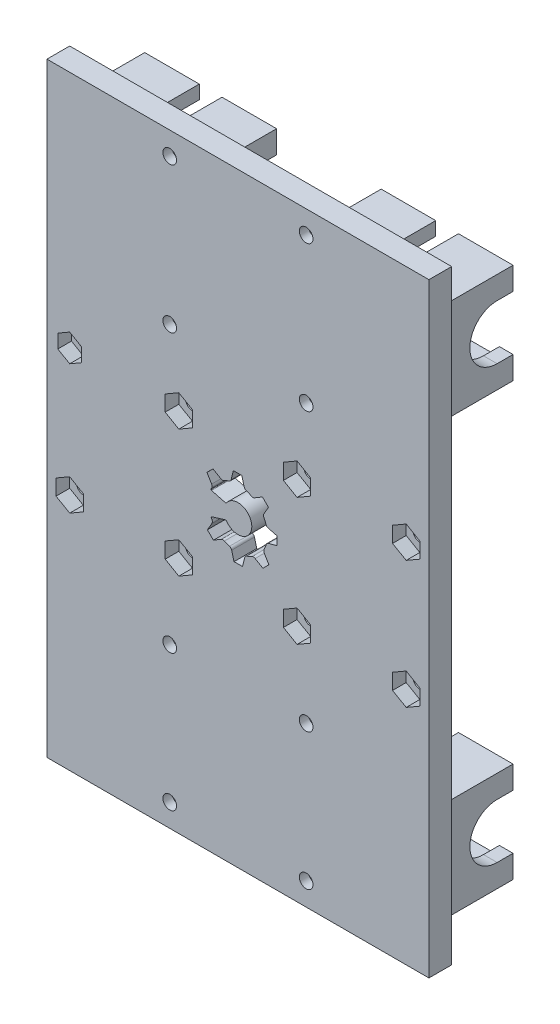
SolidWorks part; units mm, degrees
ref_plane "Alzado" through (0, 0, 0) normal (0, 0, 1) x (1, 0, 0)
ref_plane "Planta" through (0, 0, 0) normal (0, 1, 0) x (1, 0, 0)
ref_plane "Vista lateral" through (0, 0, 0) normal (1, 0, 0) x (0, 0, -1)
sketch "Croquis1" plane through (0, 0, 0) normal (0, 0, 1) x (1, 0, 0)
  line L0 (0, 0) -> (84, 0)
  line L1 (84, 0) -> (84, 133)
  line L2 (84, 133) -> (0, 133)
  line L3 (0, 133) -> (0, 0)
  circle A6 centre (57, 5) radius 1.5
  circle A7 centre (27, 5) radius 1.5
  circle A8 centre (27, 35) radius 1.5
  circle A9 centre (57, 35) radius 1.5
  circle A10 centre (57, 128) radius 1.5
  circle A11 centre (27, 128) radius 1.5
  circle A12 centre (27, 96) radius 1.5
  circle A13 centre (57, 96) radius 1.5
  circle A14 centre (5, 80.5) radius 1.5
  circle A15 centre (29, 80.5) radius 1.5
  circle A16 centre (29, 52.5) radius 1.5
  circle A17 centre (5, 52.5) radius 1.5
  circle A18 centre (79, 52.5) radius 1.5
  circle A19 centre (55, 52.5) radius 1.5
  circle A20 centre (55, 80.5) radius 1.5
  circle A21 centre (79, 80.5) radius 1.5
  dimension "D8" = 3
  dimension "D5" = 3
  dimension "D12" = 3
  dimension "D1" = 84
  dimension "D2" = 133
  dimension "D6" = 2
  dimension "D9" = 2
  dimension "D10" = 2
  dimension "D11" = 2
  dimension "D14" = 2
  dimension "D15" = 2
extrude "Saliente-Extruir1" add sketch "Croquis1" along normal blind 5
sketch "agujeros tuercas" plane through (0, 0, 0) normal (0, 0, -1) x (-1, 0, 0)
  line L44 (-57, 131) -> (-59.5981, 129.5)
  line L45 (-59.5981, 129.5) -> (-59.5981, 126.5)
  line L46 (-59.5981, 126.5) -> (-57, 125)
  line L47 (-57, 125) -> (-54.4019, 126.5)
  line L48 (-54.4019, 126.5) -> (-54.4019, 129.5)
  line L49 (-54.4019, 129.5) -> (-57, 131)
  line L50 (-27, 131) -> (-29.5981, 129.5)
  line L51 (-29.5981, 129.5) -> (-29.5981, 126.5)
  line L52 (-29.5981, 126.5) -> (-27, 125)
  line L53 (-27, 125) -> (-24.4019, 126.5)
  line L54 (-24.4019, 126.5) -> (-24.4019, 129.5)
  line L55 (-24.4019, 129.5) -> (-27, 131)
  line L68 (-27, 99) -> (-29.5981, 97.5)
  line L69 (-29.5981, 97.5) -> (-29.5981, 94.5)
  line L70 (-29.5981, 94.5) -> (-27, 93)
  line L71 (-27, 93) -> (-24.4019, 94.5)
  line L72 (-24.4019, 94.5) -> (-24.4019, 97.5)
  line L73 (-24.4019, 97.5) -> (-27, 99)
  line L164 (-57, 99) -> (-59.5981, 97.5)
  line L165 (-59.5981, 97.5) -> (-59.5981, 94.5)
  line L166 (-59.5981, 94.5) -> (-57, 93)
  line L167 (-57, 93) -> (-54.4019, 94.5)
  line L168 (-54.4019, 94.5) -> (-54.4019, 97.5)
  line L169 (-54.4019, 97.5) -> (-57, 99)
  line L218 (-57, 38) -> (-59.5981, 36.5)
  line L219 (-59.5981, 36.5) -> (-59.5981, 33.5)
  line L220 (-59.5981, 33.5) -> (-57, 32)
  line L221 (-57, 32) -> (-54.4019, 33.5)
  line L222 (-54.4019, 33.5) -> (-54.4019, 36.5)
  line L223 (-54.4019, 36.5) -> (-57, 38)
  line L224 (-27, 38) -> (-29.5981, 36.5)
  line L225 (-29.5981, 36.5) -> (-29.5981, 33.5)
  line L226 (-29.5981, 33.5) -> (-27, 32)
  line L227 (-27, 32) -> (-24.4019, 33.5)
  line L228 (-24.4019, 33.5) -> (-24.4019, 36.5)
  line L229 (-24.4019, 36.5) -> (-27, 38)
  line L230 (-57, 8) -> (-59.5981, 6.5)
  line L231 (-59.5981, 6.5) -> (-59.5981, 3.5)
  line L232 (-59.5981, 3.5) -> (-57, 2)
  line L233 (-57, 2) -> (-54.4019, 3.5)
  line L234 (-54.4019, 3.5) -> (-54.4019, 6.5)
  line L235 (-54.4019, 6.5) -> (-57, 8)
  line L236 (-27, 8) -> (-29.5981, 6.5)
  line L237 (-29.5981, 6.5) -> (-29.5981, 3.5)
  line L238 (-29.5981, 3.5) -> (-27, 2)
  line L239 (-27, 2) -> (-24.4019, 3.5)
  line L240 (-24.4019, 3.5) -> (-24.4019, 6.5)
  line L241 (-24.4019, 6.5) -> (-27, 8)
  circle A1 centre (-57, 128) radius 3 construction
  circle A2 centre (-27, 128) radius 2.5981 construction
  circle A4 centre (-57, 96) radius 3 construction
  circle A5 centre (-27, 96) radius 3 construction
  circle A14 centre (-57, 35) radius 3 construction
  circle A15 centre (-27, 35) radius 3 construction
  circle A16 centre (-57, 5) radius 3 construction
  circle A17 centre (-27, 5) radius 3 construction
sketch "Croquis3" plane through (0, 0, 0) normal (0, 0, -1) x (-1, 0, 0)
  line L0 (-82.5, 125) -> (-82.5, 103)
  line L1 (-82.5, 125) -> (-53.5, 125)
  line L2 (-82.5, 103) -> (-53.5, 103)
  line L3 (-53.5, 103) -> (-53.5, 125)
  line L4 (-84, 0) -> (-84, 133) construction
  line L5 (-84, 133) -> (0, 133) construction
  line L6 (-30.5, 125) -> (-30.5, 103)
  line L7 (-30.5, 103) -> (-1.5, 103)
  line L8 (-1.5, 103) -> (-1.5, 125)
  line L9 (-1.5, 125) -> (-30.5, 125)
  line L10 (0, 133) -> (0, 0) construction
  line L11 (10, 114) -> (-94, 114) construction
  line L17 (-82.5, 30) -> (-82.5, 8)
  line L18 (-82.5, 30) -> (-53.5, 30)
  line L19 (-82.5, 8) -> (-53.5, 8)
  line L20 (-53.5, 8) -> (-53.5, 30)
  line L21 (-30.5, 30) -> (-30.5, 8)
  line L22 (-30.5, 8) -> (-1.5, 8)
  line L23 (-1.5, 8) -> (-1.5, 30)
  line L24 (-1.5, 30) -> (-30.5, 30)
  line L25 (10, 19) -> (-94, 19) construction
  dimension "D1" = 22
  dimension "D2" = 29
  dimension "D3" = 1.5
  dimension "D4" = 8
  dimension "D5" = 1.5
  dimension "D6" = 8
  dimension "D7" = 29
  dimension "D8" = 22
  dimension "D9" = 2
extrude "Saliente-Extruir2" add sketch "Croquis3" along normal blind 15
sketch "Croquis4" plane through (1.5, 0, 0) normal (-1, 0, 0) x (0, 0, 1)
  line L0 (0, 133) -> (0, 0) construction
  line L2 (-11.5, 25) -> (-15, 25)
  line L3 (-11.5, 120) -> (-15, 120)
  line L4 (-15, 103) -> (-15, 125) construction
  line L5 (-15, 120) -> (-15, 108)
  line L6 (-15, 108) -> (-11.5, 108)
  line L7 (-15, 25) -> (-15, 13)
  line L8 (-15, 13) -> (-11.5, 13)
  arc A0 (-11.5, 108) -> (-11.5, 120) centre (-11.5, 114) ccw
  arc A1 (-11.5, 13) -> (-11.5, 25) centre (-11.5, 19) ccw
  dimension "D2" = 6
  dimension "D1" = 11.5
  dimension "D3" = 2
extrude "agujero rodamientos" cut sketch "Croquis4" against normal up to surface (81 mm away) up to face at (82.5, 114, -7.5)
ref_plane "Plano1" through (4.5, 0, 0) normal (-1, 0, 0) x (0, 0, 1)
ref_plane "Plano3" through (56.5, 0, 0) normal (-1, 0, 0) x (0, 0, 1)
sketch "Croquis5" plane through (56.5, 0, 0) normal (-1, 0, 0) x (0, 0, 1)
  line L0 (-11.5, 122) -> (-15, 122)
  line L1 (-15, 120) -> (-15, 125) construction
  line L2 (-15, 122) -> (-15, 106)
  line L4 (-11.5, 106) -> (-15, 106)
  arc A1 (-11.5, 106) -> (-11.5, 122) centre (-11.5, 114) ccw
extrude "Cortar-Extruir3" cut sketch "Croquis5" against normal offset from surface (23 mm away) 3 up to face at (82.5, 114, -9.625)
sketch "Croquis6" plane through (4.5, 0, 0) normal (-1, 0, 0) x (0, 0, 1)
  line L0 (-11.5, 122) -> (-15, 122)
  line L1 (-11.5, 106) -> (-15, 106)
  line L2 (-15, 106) -> (-15, 122)
  arc A1 (-11.5, 106) -> (-11.5, 122) centre (-11.5, 114) ccw
extrude "Cortar-Extruir4" cut sketch "Croquis6" against normal offset from surface (23 mm away) 3 up to face at (30.5, 114, -9.625)
ref_plane "Plano4" through (56.5, 0, 0) normal (-1, 0, 0) x (0, 0, 1)
sketch "Croquis7" plane through (56.5, 0, 0) normal (-1, 0, 0) x (0, 0, 1)
  line L0 (-11.5, 27) -> (-15, 27)
  line L1 (-15, 25) -> (-15, 30) construction
  line L2 (-11.5, 11) -> (-15, 11)
  line L3 (-15, 8) -> (-15, 13) construction
  line L4 (-15, 11) -> (-15, 27)
  arc A1 (-11.5, 11) -> (-11.5, 27) centre (-11.5, 19) ccw
extrude "Cortar-Extruir5" cut sketch "Croquis7" against normal offset from surface (23 mm away) 3 up to face at (82.5, 19, -9.625)
ref_plane "Plano5" through (4.5, 0, 0) normal (-1, 0, 0) x (0, 0, 1)
sketch "Croquis8" plane through (4.5, 0, 0) normal (-1, 0, 0) x (0, 0, 1)
  line L0 (-11.5, 27) -> (-15, 27)
  line L1 (-15, 27) -> (-15, 11)
  line L2 (-15, 11) -> (-11.5, 11)
  arc A1 (-11.5, 11) -> (-11.5, 27) centre (-11.5, 19) ccw
extrude "Cortar-Extruir6" cut sketch "Croquis8" against normal offset from surface (23 mm away) 3 up to face at (30.5, 19, -9.625)
sketch "Croquis9" plane through (0, 125, 0) normal (0, 1, 0) x (1, 0, 0)
  line L0 (13.5, 15) -> (18.5, 15)
  line L1 (65.5, 15) -> (70.5, 15)
  line L2 (1.5, 15) -> (30.5, 15) construction
  line L3 (18.5, 15) -> (18.5, 7.5)
  line L4 (18.5, 7.5) -> (13.5, 7.5)
  line L5 (13.5, 7.5) -> (13.5, 15)
  line L6 (13.5, 3) -> (18.5, 3)
  line L7 (18.5, 3) -> (18.5, 0)
  line L8 (84, 0) -> (0, 0) construction
  line L9 (18.5, 0) -> (13.5, 0)
  line L10 (1.5, 0) -> (30.5, 0) construction
  line L11 (13.5, 0) -> (13.5, 3)
  line L12 (53.5, 15) -> (82.5, 15) construction
  line L13 (70.5, 15) -> (70.5, 7.5)
  line L14 (70.5, 7.5) -> (65.5, 7.5)
  line L15 (65.5, 7.5) -> (65.5, 15)
  line L16 (65.5, 3) -> (70.5, 3)
  line L17 (70.5, 3) -> (70.5, 0)
  line L18 (53.5, 0) -> (82.5, 0) construction
  line L19 (70.5, 0) -> (65.5, 0)
  line L20 (65.5, 0) -> (65.5, 3)
  dimension "D1" = 4.5
  dimension "D2" = 7.5
  dimension "D3" = 5
  dimension "D5" = 7.5
  dimension "D6" = 5
extrude "Cortar-Extruir7" cut sketch "Croquis9" against normal through all
sketch "Croquis10" plane through (0, 0, 0) normal (0, 0, 1) x (1, 0, 0)
  line L0 (42, 133) -> (42, 0) construction
  line L2 (35.1881, 71.8847) -> (36.5015, 73.2203)
  line L3 (40.9908, 75.1242) -> (42.864, 75.14)
  line L4 (47.3847, 73.3119) -> (48.7203, 71.9985)
  line L5 (50.6242, 67.5092) -> (50.64, 65.636)
  line L6 (48.8119, 61.1153) -> (47.4985, 59.7797)
  line L7 (36.2096, 63.9479) -> (39.384, 64.9286)
  line L8 (35.1881, 71.8847) -> (36.2199, 70.1785)
  line L9 (43.0092, 57.8758) -> (41.136, 57.86)
  line L10 (36.6153, 59.6881) -> (35.2797, 61.0015)
  line L11 (36.5015, 73.2203) -> (38.2249, 72.2174)
  line L12 (40.9908, 75.1242) -> (40.5139, 73.1882)
  line L13 (42.864, 75.14) -> (43.3734, 73.2122)
  line L14 (47.3847, 73.3119) -> (45.6785, 72.2801)
  line L15 (48.7203, 71.9985) -> (47.7174, 70.2751)
  line L16 (50.6242, 67.5092) -> (48.6882, 67.9861)
  line L17 (50.64, 65.636) -> (48.7122, 65.1266)
  line L18 (48.8119, 61.1153) -> (47.7801, 62.8215)
  line L19 (47.4985, 59.7797) -> (45.7751, 60.7826)
  line L20 (43.0092, 57.8758) -> (43.4861, 59.8118)
  line L21 (41.136, 57.86) -> (40.6266, 59.7878)
  line L22 (36.6153, 59.6881) -> (38.3215, 60.7199)
  line L23 (35.2797, 61.0015) -> (36.2826, 62.7249)
  line L24 (39.4066, 68.1085) -> (36.1706, 68.9523)
  line L25 (84, 133) -> (0, 133) construction
  line L26 (0, 0) -> (84, 0) construction
  line L27 (84, 66.5) -> (0, 66.5) construction
  line L28 (84, 0) -> (84, 133) construction
  line L29 (0, 133) -> (0, 0) construction
  arc A0 (43.9667, 60.3256) -> (45.0717, 60.7943) centre (42, 66.5) ccw
  arc A1 (36.127, 63.7617) -> (36.2943, 63.4283) centre (42, 66.5) ccw
  arc A2 (36.2096, 63.9479) -> (36.127, 63.7617) centre (36.2495, 63.8188) ccw
  arc A3 (36.0813, 69.1381) -> (36.1706, 68.9523) centre (36.2047, 69.0831) ccw
  arc A4 (38.9283, 72.2057) -> (38.2249, 72.2174) centre (38.587, 72.8397) cw
  arc A5 (36.2434, 69.4753) -> (36.2199, 70.1785) centre (35.6038, 69.8059) ccw
  arc A6 (43.8625, 72.7066) -> (43.3734, 73.2122) centre (44.0695, 73.3962) cw
  arc A7 (40.0333, 72.6744) -> (40.5139, 73.1882) centre (39.8148, 73.3604) ccw
  arc A8 (47.7057, 69.5717) -> (47.7174, 70.2751) centre (48.3397, 69.913) cw
  arc A9 (44.9753, 72.2566) -> (45.6785, 72.2801) centre (45.3059, 72.8962) ccw
  arc A10 (48.2066, 64.6375) -> (48.7122, 65.1266) centre (48.8962, 64.4305) cw
  arc A11 (48.1744, 68.4667) -> (48.6882, 67.9861) centre (48.8604, 68.6852) ccw
  arc A12 (45.0717, 60.7943) -> (45.7751, 60.7826) centre (45.413, 60.1603) cw
  arc A13 (47.7566, 63.5247) -> (47.7801, 62.8215) centre (48.3962, 63.1941) ccw
  arc A14 (40.1375, 60.2934) -> (40.6266, 59.7878) centre (39.9305, 59.6038) cw
  arc A15 (43.9667, 60.3256) -> (43.4861, 59.8118) centre (44.1852, 59.6396) ccw
  arc A16 (36.2943, 63.4283) -> (36.2826, 62.7249) centre (35.6603, 63.087) cw
  arc A17 (39.0247, 60.7434) -> (38.3215, 60.7199) centre (38.6941, 60.1038) ccw
  arc A18 (39.0247, 60.7434) -> (40.1375, 60.2934) centre (42, 66.5) ccw
  arc A19 (36.2434, 69.4753) -> (36.0813, 69.1381) centre (42, 66.5) ccw
  arc A20 (40.0333, 72.6744) -> (38.9283, 72.2057) centre (42, 66.5) ccw
  arc A21 (44.9753, 72.2566) -> (43.8625, 72.7066) centre (42, 66.5) ccw
  arc A22 (48.1744, 68.4667) -> (47.7057, 69.5717) centre (42, 66.5) ccw
  arc A23 (47.7566, 63.5247) -> (48.2066, 64.6375) centre (42, 66.5) ccw
  arc A24 (39.384, 64.9286) -> (39.4066, 68.1085) centre (42, 66.5) ccw
  point P73 (-9.9687, -24.3356)
  point P82 (42, 66.5)
  dimension "D1" = 0.1351
  dimension "D2" = 0.1351
extrude "Cortar-Extruir11" cut sketch "agujeros tuercas" against normal blind 3
extrude "Cortar-Extruir12" cut sketch "Croquis10" along normal through all
sketch "Croquis11" plane through (0, 0, 5) normal (0, 0, 1) x (1, 0, 0)
  line L0 (4.5, 131.0223) -> (4.5, 88.2721) construction
  line L1 (5, 83.518) -> (2.3863, 82.009)
  line L2 (2.3863, 82.009) -> (2.3863, 78.991)
  line L3 (2.3863, 78.991) -> (5, 77.482)
  line L4 (5, 77.482) -> (7.6137, 78.991)
  line L5 (7.6137, 78.991) -> (7.6137, 82.009)
  line L6 (7.6137, 82.009) -> (5, 83.518)
  line L7 (29, 83.9641) -> (26, 82.2321)
  line L8 (26, 82.2321) -> (26, 78.7679)
  line L9 (26, 78.7679) -> (29, 77.0359)
  line L10 (29, 77.0359) -> (32, 78.7679)
  line L11 (32, 78.7679) -> (32, 82.2321)
  line L12 (32, 82.2321) -> (29, 83.9641)
  line L13 (55, 83.9641) -> (52, 82.2321)
  line L14 (52, 82.2321) -> (52, 78.7679)
  line L15 (52, 78.7679) -> (55, 77.0359)
  line L16 (55, 77.0359) -> (58, 78.7679)
  line L17 (58, 78.7679) -> (58, 82.2321)
  line L18 (58, 82.2321) -> (55, 83.9641)
  line L19 (79, 83.9641) -> (76, 82.2321)
  line L20 (76, 82.2321) -> (76, 78.7679)
  line L21 (76, 78.7679) -> (79, 77.0359)
  line L22 (79, 77.0359) -> (82, 78.7679)
  line L23 (82, 78.7679) -> (82, 82.2321)
  line L24 (82, 82.2321) -> (79, 83.9641)
  line L31 (55, 55.9641) -> (52, 54.2321)
  line L32 (52, 54.2321) -> (52, 50.7679)
  line L33 (52, 50.7679) -> (55, 49.0359)
  line L34 (55, 49.0359) -> (58, 50.7679)
  line L35 (58, 50.7679) -> (58, 54.2321)
  line L36 (58, 54.2321) -> (55, 55.9641)
  line L37 (29, 55.9641) -> (26, 54.2321)
  line L38 (26, 54.2321) -> (26, 50.7679)
  line L39 (26, 50.7679) -> (29, 49.0359)
  line L40 (29, 49.0359) -> (32, 50.7679)
  line L41 (32, 50.7679) -> (32, 54.2321)
  line L42 (32, 54.2321) -> (29, 55.9641)
  line L43 (5, 55.9641) -> (2, 54.2321)
  line L44 (2, 54.2321) -> (2, 50.7679)
  line L45 (2, 50.7679) -> (5, 49.0359)
  line L46 (5, 49.0359) -> (8, 50.7679)
  line L47 (8, 50.7679) -> (8, 54.2321)
  line L48 (8, 54.2321) -> (5, 55.9641)
  line L49 (4.5, 8.25) -> (4.5, -8.25) construction
  line L50 (14.5, 131.0223) -> (14.5, 88.2721) construction
  line L57 (79, 55.9641) -> (76, 54.2321)
  line L58 (76, 54.2321) -> (76, 50.7679)
  line L59 (76, 50.7679) -> (79, 49.0359)
  line L60 (79, 49.0359) -> (82, 50.7679)
  line L61 (82, 50.7679) -> (82, 54.2321)
  line L62 (82, 54.2321) -> (79, 55.9641)
  circle A0 centre (5, 80.5) radius 2.6137 construction
  circle A1 centre (29, 80.5) radius 3 construction
  circle A2 centre (55, 80.5) radius 3 construction
  circle A3 centre (79, 80.5) radius 3 construction
  circle A4 centre (79, 52.5) radius 3 construction
  circle A5 centre (55, 52.5) radius 3 construction
  circle A6 centre (29, 52.5) radius 3 construction
  circle A7 centre (5, 52.5) radius 3 construction
extrude "Cortar-Extruir13" cut sketch "Croquis11" against normal blind 3
